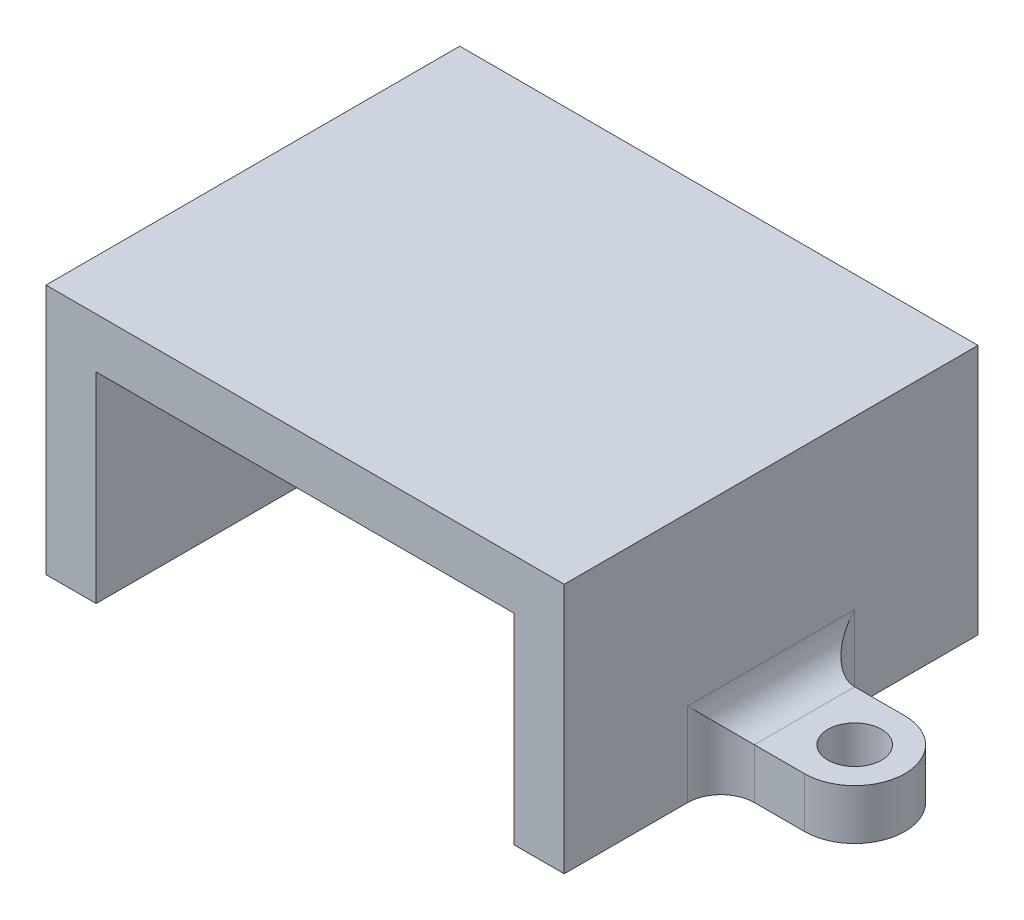
SolidWorks part; units mm, degrees
ref_plane "前视基准面" through (0, 0, 0) normal (0, 0, 1) x (1, 0, 0)
ref_plane "上视基准面" through (0, 0, 0) normal (0, 1, 0) x (1, 0, 0)
ref_plane "右视基准面" through (0, 0, 0) normal (1, 0, 0) x (0, 0, -1)
sketch "草图1" plane through (0, 0, 0) normal (0, 0, 1) x (1, 0, 0)
  line L0 (0, 0) -> (3, 0)
  line L1 (3, 0) -> (3, 12)
  line L2 (3, 12) -> (28, 12)
  line L3 (28, 12) -> (28, 0)
  line L4 (28, 0) -> (31, 0)
  line L5 (31, 0) -> (31, 15)
  line L6 (31, 15) -> (0, 15)
  line L7 (0, 15) -> (0, 0)
  dimension "D1" = 12
  dimension "D2" = 3
  dimension "D3" = 3
  dimension "D4" = 3
  dimension "D5" = 25
extrude "凸台-拉伸1" add sketch "草图1" along normal blind 24.75
sketch "草图2" plane through (0, 0, 0) normal (0, -1, 0) x (1, 0, 0)
  line L0 (15.5, 24.75) -> (15.5, -1.1402) construction
  line L1 (3, 24.75) -> (28, 24.75) construction
  line L2 (0, 12.375) -> (33.2336, 12.375) construction
  line L3 (0, 24.75) -> (0, 0) construction
  line L4 (36, 9.375) -> (31, 9.375)
  line L5 (31, 24.75) -> (31, 0) construction
  line L6 (31, 15.375) -> (31, 9.375)
  line L7 (0, 15.375) -> (0, 9.375)
  line L8 (-5, 9.375) -> (0, 9.375)
  line L9 (31, 15.375) -> (36, 15.375)
  line L10 (0, 15.375) -> (-5, 15.375)
  arc A0 (36, 9.375) -> (36, 15.375) centre (36, 12.375) ccw
  circle A1 centre (36, 12.375) radius 1.6
  circle A2 centre (-5, 12.375) radius 1.6
  arc A3 (-5, 9.375) -> (-5, 15.375) centre (-5, 12.375) cw
  dimension "D1" = 6
  dimension "D2" = 3.2
  dimension "D3" = 5
extrude "凸台-拉伸2" add sketch "草图2" against normal blind 3
fillet "圆角1" radius 2 3 edges at (31, 1.5, 9.375) (31, 1.5, 15.375) (31, 3, 12.375)
fillet "圆角2" radius 2 3 edges at (0, 1.5, 9.375) (0, 3, 12.375) (0, 1.5, 15.375)
